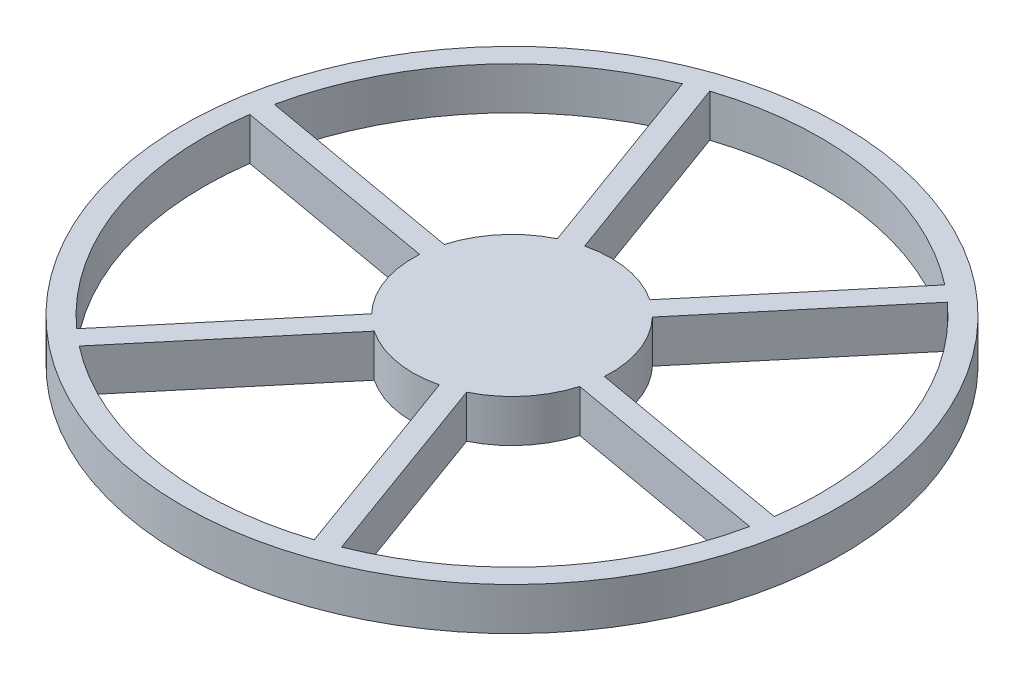
SolidWorks part; units mm, degrees
material "5052-H36"
ref_plane "Front Plane" through (0, 0, 0) normal (0, 0, 1) x (1, 0, 0)
ref_plane "Top Plane" through (0, 0, 0) normal (0, 1, 0) x (1, 0, 0)
ref_plane "Right Plane" through (0, 0, 0) normal (1, 0, 0) x (0, 0, -1)
sketch "Sketch1" plane through (0, 0, 0) normal (0, 1, 0) x (1, 0, 0)
  circle A0 centre (0, 0) radius 98.425
  dimension "D1" = 196.85
extrude "Boss-Extrude1" add sketch "Sketch1" along normal blind 12.7
sketch "Sketch2" plane through (0, 12.7, 0) normal (0, 1, 0) x (1, 0, 0)
  line L0 (0, 0) -> (63.2664, 75.3979) construction
  line L1 (0, 0) -> (0, 92.075) construction
  line L14 (21.3833, 20.5441) -> (61.5817, 68.4507)
  line L16 (16.5189, 24.6258) -> (56.7173, 72.5324)
  line L18 (-7.1001, 28.7905) -> (-28.4893, 87.5567)
  line L19 (-13.0672, 26.6187) -> (-34.4563, 85.3848)
  line L20 (-28.4834, 8.2464) -> (-90.0709, 19.1059)
  line L21 (-29.586, 1.9928) -> (-91.1736, 12.8524)
  line L22 (-21.3833, -20.5441) -> (-61.5817, -68.4507)
  line L23 (-16.5189, -24.6258) -> (-56.7173, -72.5324)
  line L24 (7.1001, -28.7905) -> (28.4893, -87.5567)
  line L25 (13.0672, -26.6187) -> (34.4563, -85.3848)
  line L26 (28.4834, -8.2464) -> (90.0709, -19.1059)
  line L27 (29.586, -1.9928) -> (91.1736, -12.8524)
  arc A0 (-13.0672, 26.6187) -> (-28.4834, 8.2464) centre (0, 0) ccw
  arc A1 (16.5189, 24.6258) -> (-7.1001, 28.7905) centre (0, 0) ccw
  arc A2 (-29.586, 1.9928) -> (-21.3833, -20.5441) centre (0, 0) ccw
  circle A3 centre (0, 0) radius 92.075
  arc A4 (91.1736, -12.8524) -> (61.5817, 68.4507) centre (0, 0) ccw
  arc A5 (-16.5189, -24.6258) -> (7.1001, -28.7905) centre (0, 0) ccw
  arc A6 (13.0672, -26.6187) -> (28.4834, -8.2464) centre (0, 0) ccw
  arc A7 (29.586, -1.9928) -> (21.3833, 20.5441) centre (0, 0) ccw
  arc A8 (56.7173, 72.5324) -> (-28.4893, 87.5567) centre (0, 0) ccw
  arc A9 (-34.4563, 85.3848) -> (-90.0709, 19.1059) centre (0, 0) ccw
  arc A10 (-91.1736, 12.8524) -> (-61.5817, -68.4507) centre (0, 0) ccw
  arc A11 (-56.7173, -72.5324) -> (28.4893, -87.5567) centre (0, 0) ccw
  arc A12 (34.4563, -85.3848) -> (90.0709, -19.1059) centre (0, 0) ccw
  circle A13 centre (0, 0) radius 98.425 construction
  dimension "D3" = 29.6531
  dimension "D2" = 6.35
  dimension "D4" = 3.175
  dimension "D5" = 40
  dimension "D1" = 6.35
extrude "Cut-Extrude1" cut sketch "Sketch2" against normal through all
